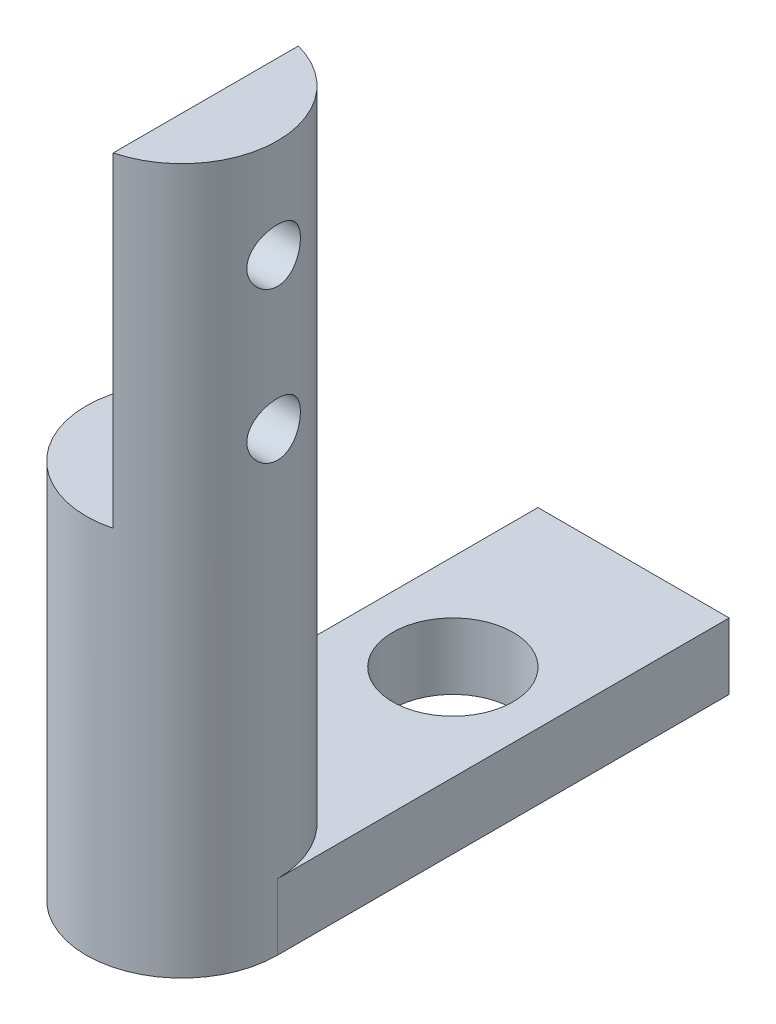
SolidWorks part; units mm, degrees
ref_plane "Front" through (0, 0, 0) normal (0, 0, 1) x (1, 0, 0)
ref_plane "Top" through (0, 0, 0) normal (0, 1, 0) x (1, 0, 0)
ref_plane "Right" through (0, 0, 0) normal (1, 0, 0) x (0, 0, -1)
sketch "草图1" plane through (0, 0, 0) normal (0, 1, 0) x (1, 0, 0)
  circle A0 centre (0, 0) radius 3.175
extrude "凸台-拉伸1" add sketch "草图1" along normal blind 57.15
sketch "草图2" plane through (0, 57.15, 0) normal (0, 1, 0) x (1, 0, 0)
  line L0 (0, 0) -> (0, 3.175) construction
  line L1 (-0.794, 3.175) -> (0.794, 3.175)
  line L2 (0.794, 3.175) -> (0.794, -3.175)
  line L3 (0.794, -3.175) -> (-3.175, -3.175)
  line L4 (-3.175, -3.175) -> (-3.175, 3.175)
  line L5 (-3.175, 3.175) -> (-0.794, 3.175)
  line L6 (0, 0) -> (0.794, 0) construction
  circle A0 centre (0, 0) radius 3.175 construction
  point P8 (0, 3.175)
extrude "切除-拉伸1" cut sketch "草图2" against normal blind 10.795
sketch "草图3" plane through (0.794, 0, 0) normal (-1, 0, 0) x (0, 0, 1)
  line L0 (0, 57.15) -> (0, 53.855) construction
  line L1 (3.0741, 57.15) -> (-3.0741, 57.15) construction
  line L2 (0, 57.15) -> (0, 48.855) construction
  line L3 (0, 53.855) -> (0, 57.15) construction
  circle A0 centre (0, 53.855) radius 0.889
  circle A1 centre (0, 48.855) radius 0.889
extrude "切除-拉伸2" cut sketch "草图3" against normal blind 10.795
sketch "草图4" plane through (0, 0, 0) normal (0, -1, 0) x (1, 0, 0)
  circle A0 centre (0, 0) radius 3.175
extrude "切除-拉伸3" cut sketch "草图4" against normal blind 34.83
sketch "草图5" plane through (0, 34.83, 0) normal (0, -1, 0) x (1, 0, 0)
  line L0 (0, 0) -> (3.175, 0) construction
  line L1 (3.175, 0) -> (3.175, -15) construction
  line L2 (3.175, -15) -> (-3.175, -15) construction
  line L3 (-3.175, -15) -> (-3.175, 0) construction
  line L4 (0, -15) -> (0, -9) construction
  line L6 (3.175, 0) -> (3.175, -15)
  line L7 (3.175, -15) -> (-3.175, -15)
  line L8 (-3.175, -15) -> (-3.175, 0)
  line L9 (0, -9) -> (0, 0) construction
  circle A0 centre (0, 0) radius 3.175 construction
  circle A1 centre (0, -9) radius 2
  arc A2 (3.175, 0) -> (-3.175, 0) centre (0, 0) ccw
extrude "凸台-拉伸2" add sketch "草图5" along normal mid plane 2.2
